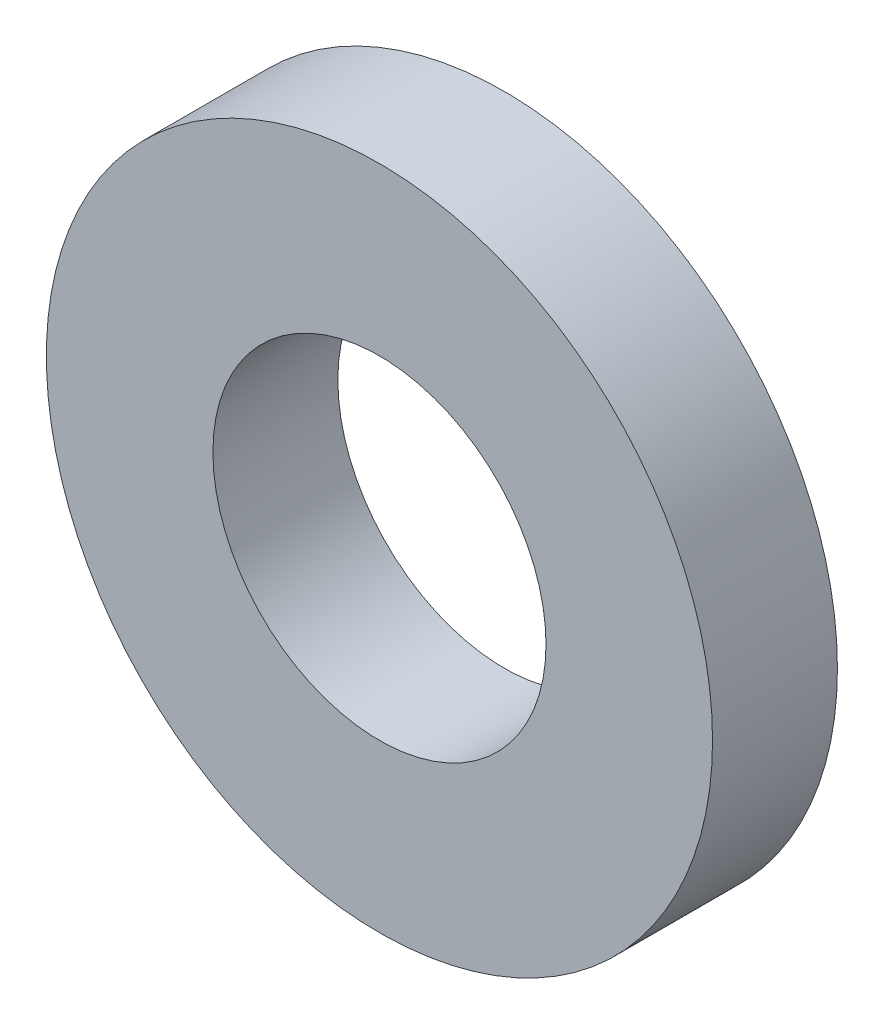
SolidWorks part; units mm, degrees
ref_plane "Front Plane" through (0, 0, 0) normal (0, 0, 1) x (1, 0, 0)
ref_plane "Top Plane" through (0, 0, 0) normal (0, 1, 0) x (1, 0, 0)
ref_plane "Right Plane" through (0, 0, 0) normal (1, 0, 0) x (0, 0, -1)
sketch "Sketch1" plane through (0, 0, 0) normal (0, 0, 1) x (1, 0, 0)
  circle A0 centre (0, 0) radius 8
  circle A1 centre (0, 0) radius 4
  dimension "D1" = 8
  dimension "D2" = 16
extrude "Boss-Extrude1" add sketch "Sketch1" along normal blind 3
